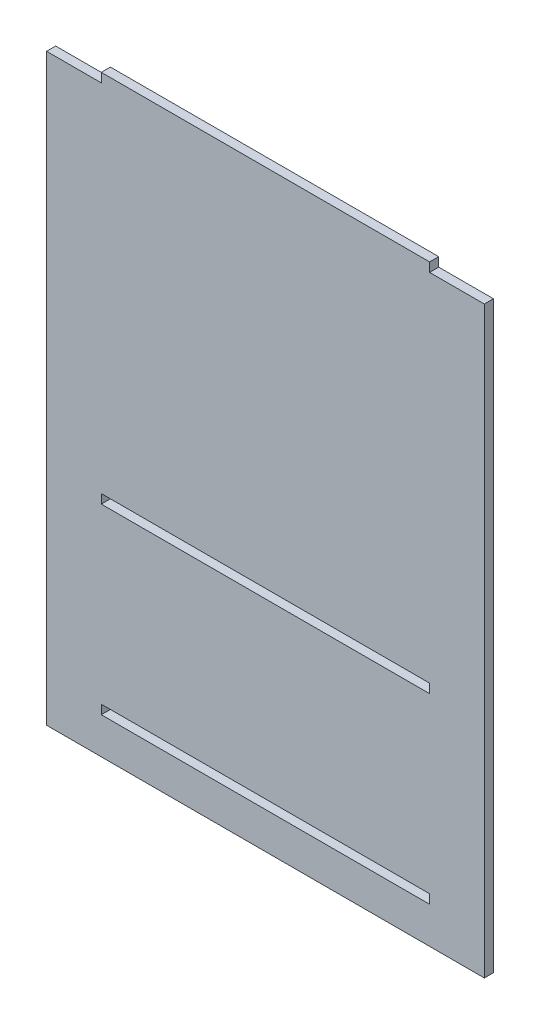
SolidWorks part; units mm, degrees
ref_plane "Front" through (0, 0, 0) normal (0, 0, 1) x (1, 0, 0)
ref_plane "Top" through (0, 0, 0) normal (0, 1, 0) x (1, 0, 0)
ref_plane "Right" through (0, 0, 0) normal (1, 0, 0) x (0, 0, -1)
sketch "Sketch2" plane through (0, 0, 0) normal (0, 0, 1) x (1, 0, 0)
  line L0 (133.35, 0) -> (152.4, 0)
  line L1 (0, 0) -> (19.05, 0)
  line L2 (0, 0) -> (0, 203.2)
  line L3 (0, 203.2) -> (19.05, 203.2)
  line L4 (152.4, 0) -> (152.4, 203.2)
  line L9 (19.05, 0) -> (133.35, 0)
  line L10 (19.05, 15.875) -> (133.35, 15.875)
  line L11 (19.05, 15.875) -> (19.05, 12.7)
  line L12 (19.05, 12.7) -> (133.35, 12.7)
  line L13 (133.35, 15.875) -> (133.35, 12.7)
  line L15 (19.05, 203.2) -> (19.05, 206.375)
  line L16 (19.05, 206.375) -> (133.35, 206.375)
  line L17 (133.35, 203.2) -> (133.35, 206.375)
  line L18 (133.35, 203.2) -> (152.4, 203.2)
  line L20 (19.05, 79.375) -> (133.35, 79.375)
  line L21 (19.05, 79.375) -> (19.05, 76.2)
  line L22 (19.05, 76.2) -> (133.35, 76.2)
  line L23 (133.35, 79.375) -> (133.35, 76.2)
  dimension "D1" = 152.4
  dimension "D2" = 203.2
  dimension "D3" = 12.7
  dimension "D4" = 3.175
  dimension "D5" = 114.3
  dimension "D6" = 19.05
  dimension "D7" = 114.3
  dimension "D8" = 19.05
  dimension "D9" = 3.175
  dimension "D10" = 3.175
  dimension "D11" = 114.3
  dimension "D12" = 19.05
  dimension "D13" = 76.2
extrude "Boss-Extrude1" add sketch "Sketch2" along normal blind 3.175
